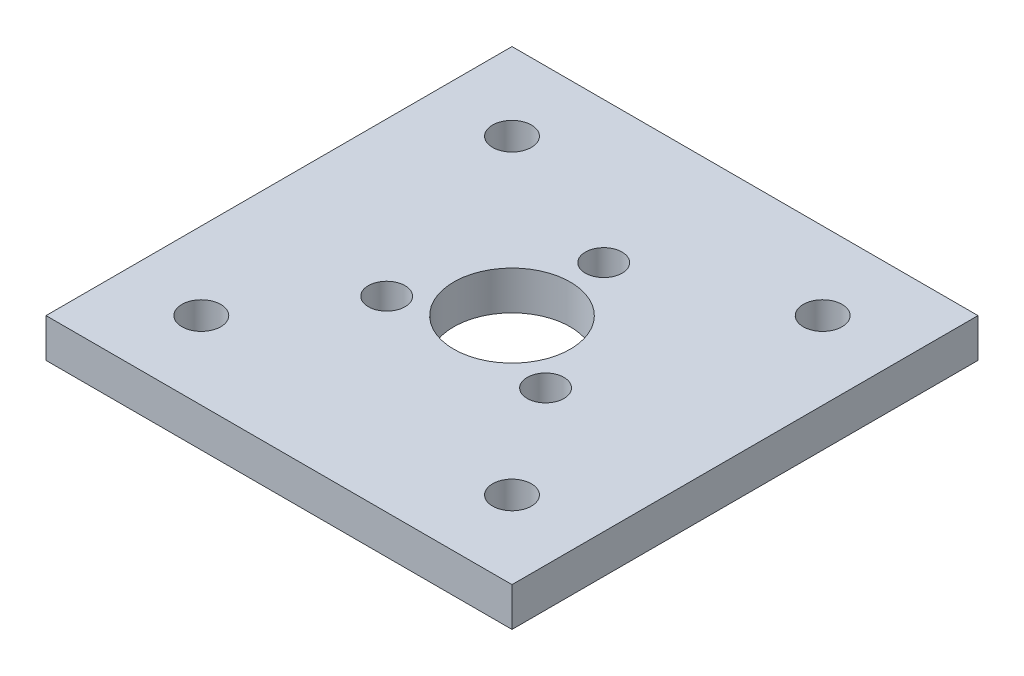
SolidWorks part; units mm, degrees
ref_plane "Front Plane" through (0, 0, 0) normal (0, 0, 1) x (1, 0, 0)
ref_plane "Top Plane" through (0, 0, 0) normal (0, 1, 0) x (1, 0, 0)
ref_plane "Right Plane" through (0, 0, 0) normal (1, 0, 0) x (0, 0, -1)
sketch "Sketch1" plane through (0, 0, 0) normal (0, 1, 0) x (1, 0, 0)
  line L1 (-19.05, -19.05) -> (19.05, -19.05)
  line L2 (-19.05, -19.05) -> (-19.05, 19.05)
  line L3 (-19.05, 19.05) -> (19.05, 19.05)
  line L4 (19.05, -19.05) -> (19.05, 19.05)
  line L5 (-19.05, -19.05) -> (19.05, 19.05) construction
  line L6 (-19.05, 19.05) -> (19.05, -19.05) construction
  circle A0 centre (0, 0) radius 19.05 construction
  dimension "D1" = 38.1
  dimension "D2" = 38.1
  dimension "D3" = 38.1
extrude "Boss-Extrude1" add sketch "Sketch1" along normal blind 3.175
sketch "Sketch2" plane through (0, 3.175, 0) normal (0, 1, 0) x (1, 0, 0)
  circle A0 centre (0, 0) radius 7.5 construction
  circle A1 centre (0, 7.5) radius 1.5
  circle A2 centre (6.4952, -3.75) radius 1.5
  circle A3 centre (-6.4952, -3.75) radius 1.5
  circle A4 centre (0, 0) radius 4.7625
  point P11 (0, 0)
  dimension "D2" = 15
  dimension "D3" = 3
  dimension "D4" = 9.525
  dimension "D1" = 3
extrude "Cut-Extrude1" cut sketch "Sketch2" against normal through all contours A1 | A3 | A2 | A4
sketch "Sketch3" plane through (0, 3.175, 0) normal (0, 1, 0) x (1, 0, 0)
  line L1 (-12.7, -12.7) -> (12.7, -12.7) construction
  line L2 (-12.7, -12.7) -> (-12.7, 12.7) construction
  line L3 (-12.7, 12.7) -> (12.7, 12.7) construction
  line L4 (12.7, -12.7) -> (12.7, 12.7) construction
  line L5 (-12.7, -12.7) -> (12.7, 12.7) construction
  line L6 (-12.7, 12.7) -> (12.7, -12.7) construction
  circle A0 centre (-12.7, 12.7) radius 1.5875
  circle A1 centre (12.7, 12.7) radius 1.5875
  circle A2 centre (12.7, -12.7) radius 1.5875
  circle A3 centre (-12.7, -12.7) radius 1.5875
  point P0 (0, 0)
  dimension "D3" = 3.175
  dimension "D1" = 25.4
  dimension "D2" = 25.4
  dimension "D4" = 2
  dimension "D5" = 2
extrude "Cut-Extrude2" cut sketch "Sketch3" against normal through all contours A0 | A3 | A2 | A1
equation "\"D3@Sketch1\"=\"D2@Sketch1\""
equation "\"D2@Sketch3\"=\"D1@Sketch3\""
